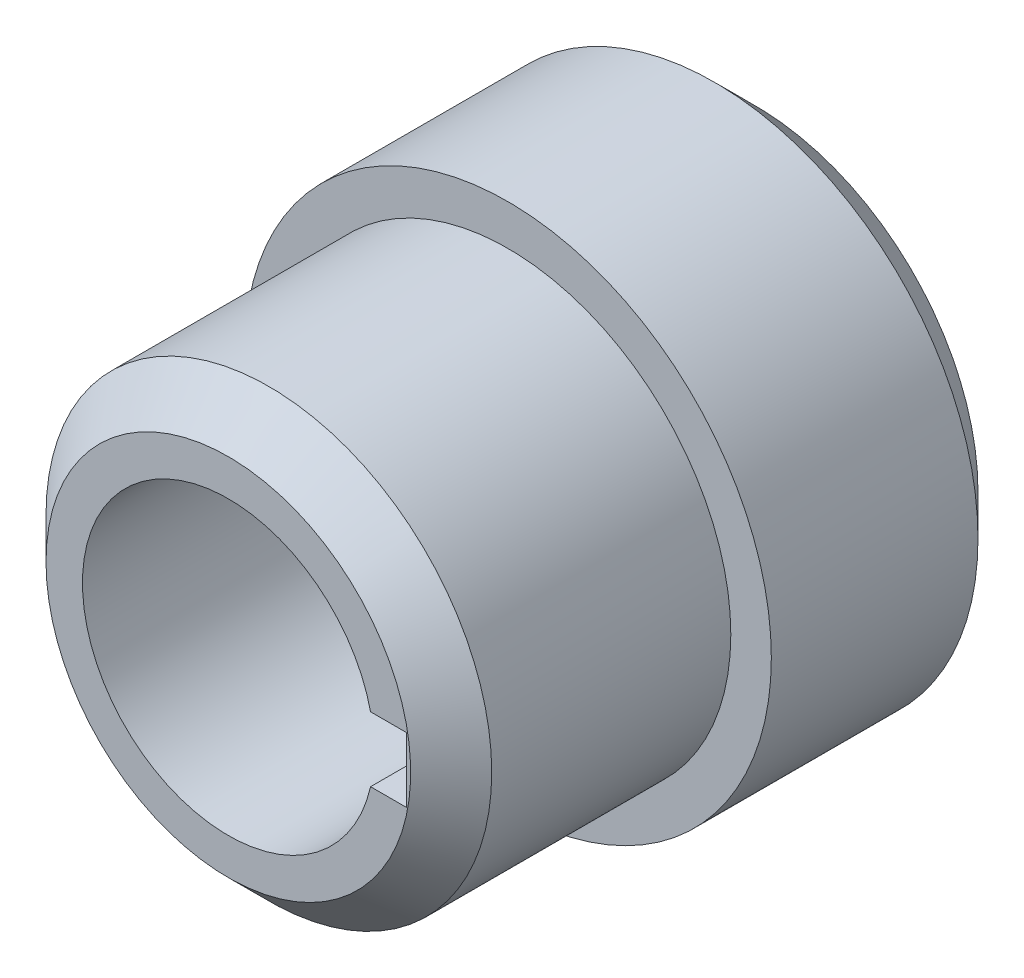
SolidWorks part; units mm, degrees
ref_plane "Přední rovina" through (0, 0, 0) normal (0, 0, 1) x (1, 0, 0)
ref_plane "Horní rovina" through (0, 0, 0) normal (0, 1, 0) x (1, 0, 0)
ref_plane "Pravá rovina" through (0, 0, 0) normal (1, 0, 0) x (0, 0, -1)
sketch "Skica1" plane through (0, 0, 0) normal (1, 0, 0) x (0, 0, -1)
  line L0 (-25.5177, 0) -> (160.4589, 0) construction
  line L1 (0, 18) -> (0, 27.5)
  line L2 (0, 27.5) -> (34.5, 27.5)
  line L3 (34.5, 27.5) -> (34.5, 32.5)
  line L4 (34.5, 32.5) -> (65, 32.5)
  line L5 (65, 32.5) -> (65, 18)
  line L6 (0, 18) -> (65, 18)
  dimension "D1" = 55
  dimension "D2" = 65
  dimension "D3" = 65
  dimension "D4" = 30.5
  dimension "D5" = 36
revolve "Rotovat1" add sketch "Skica1" angle 360 about L0
chamfer "Zkosení1" distance 5 angle 45 1 edges at (27.5, 0, 0)
chamfer "Zkosení2" distance 5 angle 45 1 edges at (32.5, 0, -65)
sketch "Skica3" plane through (0, 0, 0) normal (0, 0, 1) x (1, 0, 0)
  line L0 (-7.4201, 0) -> (47.3927, 0) construction
  line L2 (14, 4) -> (22, 4)
  line L3 (14, 4) -> (14, -4)
  line L4 (14, -4) -> (22, -4)
  line L5 (22, 4) -> (22, -4)
  circle A0 centre (0, 0) radius 18 construction
  point P9 (-18, 0)
  dimension "D1" = 32
  dimension "D2" = 8
  dimension "D3" = 8
extrude "Odebrat vysunutím1" cut sketch "Skica3" against normal through all
